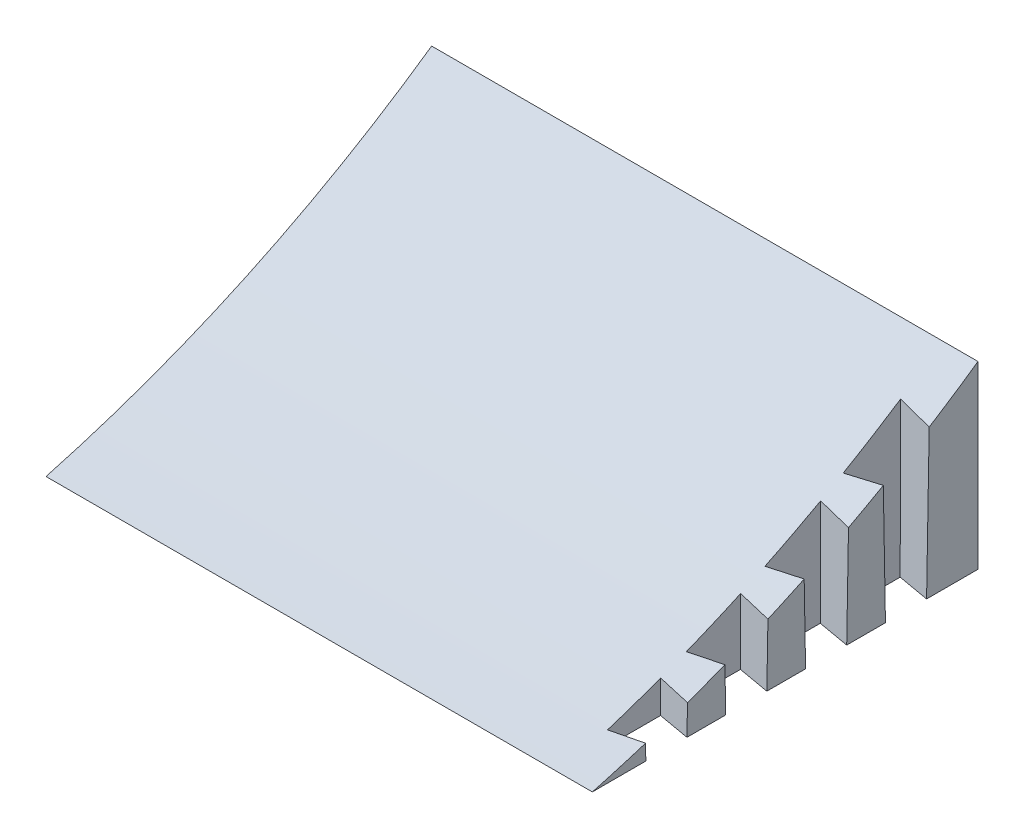
SolidWorks part; units mm, degrees
ref_plane "Front Plane" through (0, 0, 0) normal (0, 0, 1) x (1, 0, 0)
ref_plane "Top Plane" through (0, 0, 0) normal (0, 1, 0) x (1, 0, 0)
ref_plane "Right Plane" through (0, 0, 0) normal (1, 0, 0) x (0, 0, -1)
sketch "Sketch3" plane through (0, 0, 0) normal (1, 0, 0) x (0, 0, -1)
  line L0 (0, 0) -> (95.25, 0)
  line L1 (95.25, 0) -> (95.25, 44.45)
  arc A0 (0, 0) -> (95.25, 44.45) centre (-79.3399, 294.2927) ccw
  dimension "D3" = 304.8
  dimension "D1" = 44.45
  dimension "D2" = 95.25
extrude "Boss-Extrude1" add sketch "Sketch3" along normal blind 134.9375
sketch "Sketch4" plane through (0, 0, 0) normal (-1, 0, 0) x (0, 0, 1)
  line L0 (-95.25, 0) -> (-95.25, 44.45) construction
  line L1 (-95.25, 26.67) -> (-69.85, 26.67)
  line L2 (-95.25, 26.67) -> (-95.25, 7.62)
  line L3 (-95.25, 7.62) -> (-69.85, 7.62)
  line L4 (-69.85, 26.67) -> (-69.85, 7.62)
  line L5 (0, 0) -> (-95.25, 0) construction
  dimension "D1" = 25.4
  dimension "D2" = 7.62
  dimension "D3" = 19.05
extrude "Cut-Extrude1" cut sketch "Sketch4" against normal blind 6.35
sketch "Sketch5" plane through (6.35, 0, 0) normal (-1, 0, 0) x (0, 0, 1)
  line L0 (-69.85, 26.67) -> (-95.25, 26.67) construction
  line L1 (-95.25, 26.67) -> (-95.25, 7.62) construction
  circle A0 centre (-82.55, 17.145) radius 2.921
  dimension "D2" = 12.7
  dimension "D3" = 5.842
  dimension "D1" = 9.525
extrude "Cut-Extrude2" cut sketch "Sketch5" against normal blind 25.4
sketch "Sketch6" plane through (0, 0, 0) normal (0, -1, 0) x (1, 0, 0)
  line L0 (134.9375, -82.55) -> (127.0147, -83.947)
  line L1 (134.9375, 0) -> (134.9375, -95.25) construction
  line L2 (127.0147, -83.947) -> (127.0147, -70.993)
  line L3 (127.0147, -70.993) -> (134.9375, -72.39)
  line L4 (134.9375, -72.39) -> (134.9375, -82.55)
  line L5 (134.9375, -62.8227) -> (127.0147, -64.2197)
  line L6 (127.0147, -64.2197) -> (127.0147, -51.2657)
  line L7 (127.0147, -51.2657) -> (134.9375, -52.6627)
  line L8 (134.9375, -52.6627) -> (134.9375, -62.8227)
  line L9 (134.9375, -43.0953) -> (127.0147, -44.4923)
  line L10 (127.0147, -44.4923) -> (127.0147, -31.5383)
  line L11 (127.0147, -31.5383) -> (134.9375, -32.9353)
  line L12 (134.9375, -32.9353) -> (134.9375, -43.0953)
  line L13 (134.9375, -23.368) -> (127.0147, -24.765)
  line L14 (127.0147, -24.765) -> (127.0147, -11.811)
  line L15 (127.0147, -11.811) -> (134.9375, -13.208)
  line L16 (134.9375, -13.208) -> (134.9375, -23.368)
  line L18 (134.9375, -95.25) -> (0, -95.25) construction
  dimension "D1" = 80
  dimension "D2" = 80
  dimension "D4" = 12.7
  dimension "D5" = 12.954
  dimension "D6" = 10.16
  dimension "D7" = 13.208
  dimension "D3" = 4
extrude "Cut-Extrude3" cut sketch "Sketch6" against normal blind 38.1 draft 1 draft outward yes
